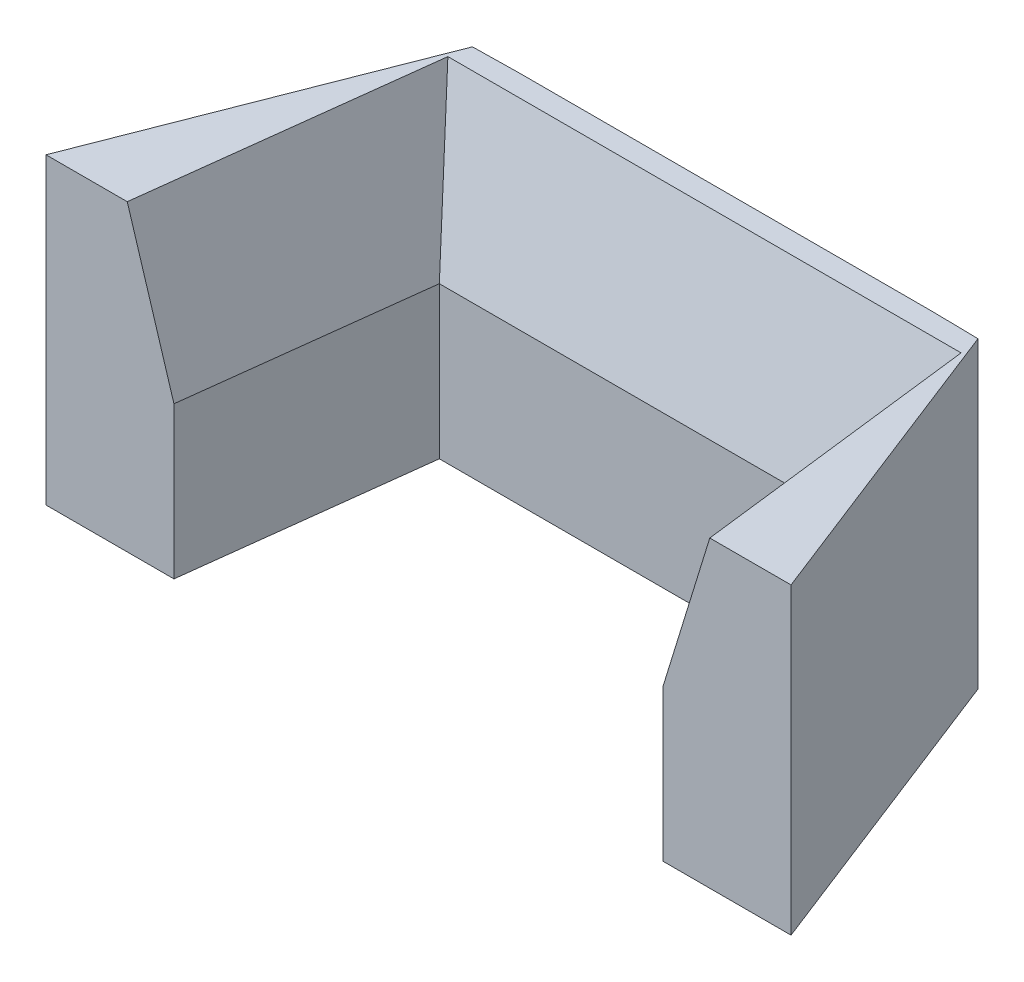
SolidWorks part; units mm, degrees
ref_plane "Front Plane" through (0, 0, 0) normal (0, 0, 1) x (1, 0, 0)
ref_plane "Top Plane" through (0, 0, 0) normal (0, 1, 0) x (1, 0, 0)
ref_plane "Right Plane" through (0, 0, 0) normal (1, 0, 0) x (0, 0, -1)
sketch "Croquis2" plane through (0, 0, 0) normal (0, 1, 0) x (1, 0, 0)
  line L0 (-0.2069, 35.333) -> (-14, 0)
  line L1 (-14, 0) -> (0, 0)
  line L2 (0, 0) -> (4.2931, 35.4086)
  line L3 (4.2931, 35.4086) -> (-0.2069, 35.333)
  line L4 (45.2931, 35.4086) -> (4.2931, 35.4086)
  line L5 (24.7931, 35.4086) -> (24.7931, 17.6731) construction
  line L6 (45.2931, 35.4086) -> (49.7931, 35.333)
  line L7 (49.5861, 0) -> (45.2931, 35.4086)
  line L8 (63.5861, 0) -> (49.5861, 0)
  line L9 (49.7931, 35.333) -> (63.5861, 0)
  line L10 (3.4443, 28.4086) -> (46.1418, 28.4086)
  dimension "D1" = 14
  dimension "D2" = 35.4086
  dimension "D3" = 35.333
  dimension "D4" = 68.676
  dimension "D5" = 4.5
  dimension "D6" = 50
  dimension "D7" = 7
extrude "Saliente-Extruir1" add sketch "Croquis2" along normal blind 30 contours L2 L3 L0 L1 | L5 L4 L2 L10 | L4 L5 L10 L7 | L9 L6 L7 L8
sketch "Croquis4" plane through (0, 0, 0) normal (1, 0, 0) x (0, 0, -1)
  line L0 (0, 0) -> (5, 0)
  line L1 (5, 0) -> (5, 30)
  line L2 (5, 30) -> (-4.9066, 30)
  line L3 (-4.9066, 30) -> (-4.9066, 0)
  line L4 (-4.9066, 0) -> (0, 0)
  dimension "D1" = 9.9066
  dimension "D2" = 5
  dimension "D3" = 30
extrude "Cortar-Extruir2" cut sketch "Croquis4" against normal mid plane 180
sketch "Croquis5" plane through (0, 0, 0) normal (0, -1, 0) x (-1, 0, 0)
  line L0 (-14.7931, 31.4086) -> (-34.7931, 31.4086)
  line L1 (-14.7931, 31.4086) -> (-14.7931, 33.4086)
  line L2 (-34.7931, 31.4086) -> (-34.7931, 33.4086)
  line L3 (-14.7931, 33.4086) -> (-34.7931, 33.4086)
  line L4 (-14.7931, 31.4086) -> (-34.7931, 33.4086) construction
  line L5 (-34.7931, 31.4086) -> (-14.7931, 33.4086) construction
  line L6 (-3.4443, 28.4086) -> (-3.4443, 35.3943) construction
  line L7 (-4.2931, 35.4086) -> (0.2069, 35.333) construction
  line L8 (-3.4443, 28.4086) -> (-46.1418, 28.4086) construction
  line L9 (-45.2931, 35.4086) -> (-4.2931, 35.4086) construction
  point P1 (-24.7931, 32.4086)
  point P12 (-24.7931, 31.4086)
  point P15 (-24.7931, 28.4086)
  dimension "D1" = 2
  dimension "D2" = 20
  dimension "D3" = 2
extrude "Saliente-Extruir2" add sketch "Croquis5" along normal blind 3
chamfer "Chaflán1" distance 15 angle 17 1 edges at (2.0253, 30, -16.7043)
chamfer "Chaflán2" distance 15 angle 17 1 edges at (47.5608, 30, -16.7043)
chamfer "Chaflán3" distance 15 angle 18 1 edges at (24.7931, 30, -28.4086)
